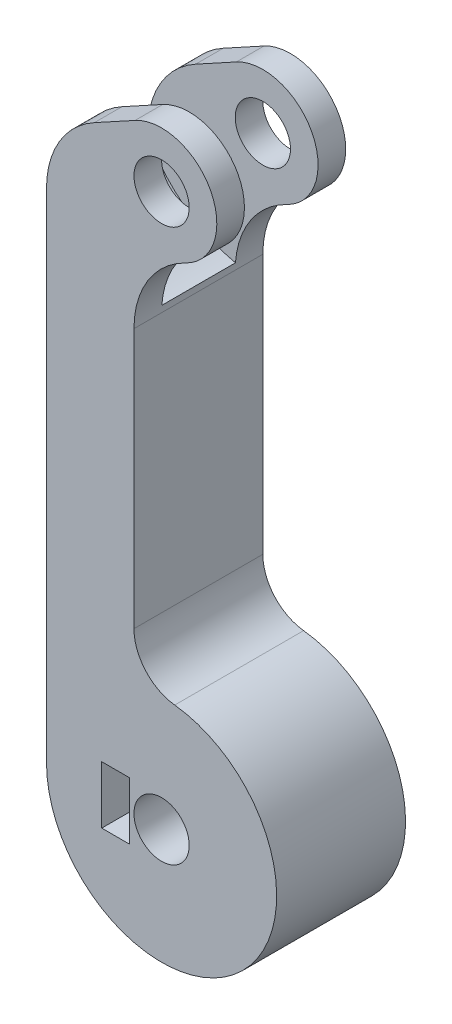
SolidWorks part; units mm, degrees
ref_plane "Alzado" through (0, 0, 0) normal (0, 0, 1) x (1, 0, 0)
ref_plane "Planta" through (0, 0, 0) normal (0, 1, 0) x (1, 0, 0)
ref_plane "Vista lateral" through (0, 0, 0) normal (1, 0, 0) x (0, 0, -1)
sketch "Croquis1" plane through (0, 0, 0) normal (0, 0, 1) x (1, 0, 0)
  line L0 (0, 0) -> (0, 60) construction
  line L1 (-12.5, 60) -> (-12.5, 0)
  line L2 (-3, 0) -> (-3, 60)
  line L3 (-12.5, 60) -> (-2.88, 65.2636)
  circle A0 centre (0, 0) radius 12.5
  circle A1 centre (0, 0) radius 3
  circle A2 centre (0, 60) radius 12.5
  circle A3 centre (0, 60) radius 3
  circle A4 centre (0, 60) radius 6
  dimension "D1" = 6
  dimension "D2" = 25
  dimension "D3" = 6
  dimension "D4" = 25
  dimension "D7" = 12
  dimension "D5" = 60
  dimension "D6" = 9.5
extrude "Saliente-Extruir1" add sketch "Croquis1" along normal blind 14 contours A4 L3 A2 L2 | A2 L1 A0 L2 | L0 A1 L2 A0 | L0 A4 L2 A3 | A4 L0 A3 L2 | A1 L0 A0 L2
fillet "Redondeo1" radius 10 1 edges at (-12.5, 60, 7)
fillet "Redondeo2" radius 10 1 edges at (-3, 54.8038, 7)
fillet "Redondeo3" radius 5 1 edges at (-3, 12.1347, 7)
sketch "Croquis2" plane through (0, 0, 14) normal (0, 0, 1) x (1, 0, 0)
  circle A0 centre (0, 60) radius 14
  dimension "D1" = 28
extrude "Cortar-Extruir1" cut sketch "Croquis2" against normal blind 8 from offset 3 offset against normal yes
sketch "Croquis3" plane through (-12.5, 0, 0) normal (-1, 0, 0) x (0, 0, 1)
  line L0 (7, 53.6952) -> (7, 0) construction
  line L1 (11, 53.6952) -> (3, 53.6952) construction
  line L2 (14, 0) -> (0, 0) construction
  circle A0 centre (7, 0) radius 1.5
  dimension "D1" = 3
extrude "Cortar-Extruir2" cut sketch "Croquis3" against normal blind 10
sketch "Croquis4" plane through (-12.5, 0, 0) normal (-1, 0, 0) x (0, 0, 1)
  circle A0 centre (7, 0) radius 5
  dimension "D1" = 10
extrude "Cortar-Extruir3" cut sketch "Croquis4" against normal blind 3
sketch "Croquis5" plane through (-9.5, 0, 0) normal (-1, 0, 0) x (0, 0, 1)
  line L0 (14, -12.5) -> (14, 12.4181) construction
  line L1 (10.6084, 0) -> (8.8042, 3.125)
  line L2 (8.8042, 3.125) -> (5.1958, 3.125)
  line L3 (5.1958, 3.125) -> (3.3916, 0)
  line L4 (3.3916, 0) -> (5.1958, -3.125)
  line L5 (5.1958, -3.125) -> (8.8042, -3.125)
  line L6 (8.8042, -3.125) -> (10.6084, 0)
  line L7 (8.8042, 3.125) -> (14, 3.125)
  line L8 (8.8042, 3.125) -> (8.8042, -3.125)
  line L9 (8.8042, -3.125) -> (14, -3.125)
  line L10 (14, 3.125) -> (14, -3.125)
  circle A0 centre (7, 0) radius 3.125 construction
  circle M1 centre (7, 0) radius 5
  circle M2 centre (7, 0) radius 1.5
extrude "Cortar-Extruir4" cut sketch "Croquis5" against normal blind 3 from offset 3 contours L8 L2 L3 L4 L5 M2 | L1 L8 L6 | L6 L9 L7 L1 M1 | L10 L7 L9 M1
